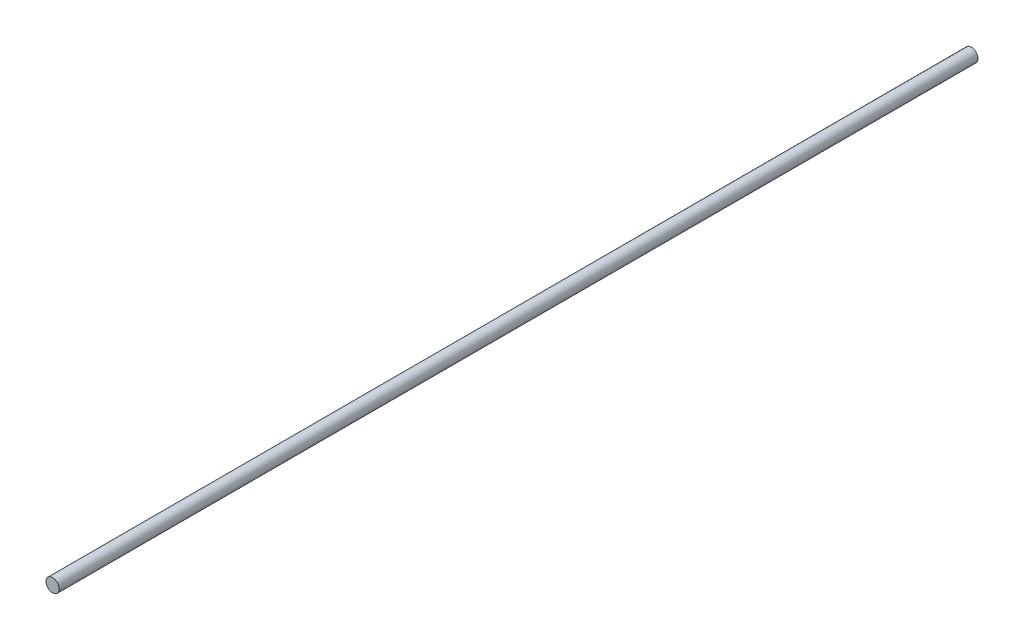
SolidWorks part; units mm, degrees
material "AISI 316L Acero inoxidable"
ref_plane "Alzado" through (0, 0, 0) normal (0, 0, 1) x (1, 0, 0)
ref_plane "Planta" through (0, 0, 0) normal (0, 1, 0) x (1, 0, 0)
ref_plane "Vista lateral" through (0, 0, 0) normal (1, 0, 0) x (0, 0, -1)
sketch "Croquis1" plane through (0, 0, 0) normal (0, 0, 1) x (1, 0, 0)
  circle A0 centre (0, 0) radius 4
  dimension "D1" = 8
extrude "Saliente-Extruir1" add sketch "Croquis1" against normal blind 555
